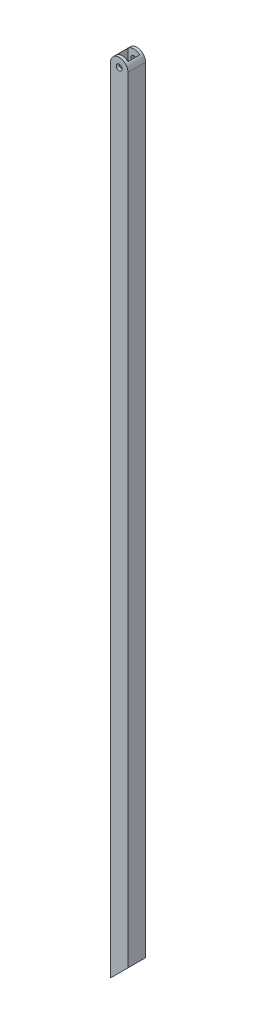
SolidWorks part; units mm, degrees
material "6061-T6 (SS)"
ref_plane "Plan de face" through (0, 0, 0) normal (0, 0, 1) x (1, 0, 0)
ref_plane "Plan de dessus" through (0, 0, 0) normal (0, 1, 0) x (1, 0, 0)
ref_plane "Plan de droite" through (0, 0, 0) normal (1, 0, 0) x (0, 0, -1)
sketch "Esquisse1" plane through (0, 0, 0) normal (0, 0, 1) x (1, 0, 0)
  line L0 (0, 0) -> (19.05, 19.05)
  line L2 (0, 0) -> (0, 860.475)
  line L4 (19.05, 19.05) -> (19.05, 860.475)
  line L5 (0, 0) -> (50000, 0) construction
  arc A0 (19.05, 860.475) -> (0, 860.475) centre (9.525, 860.475) ccw
  circle A1 centre (9.525, 860.475) radius 3.175
  dimension "D2" = 9.525
  dimension "D5" = 6.35
  dimension "D1" = 860.475
  dimension "D3" = 45
  dimension "D4" = 19.05
extrude "Boss.-Extru.1" add sketch "Esquisse1" along normal blind 19.05
sketch "Esquisse2" plane through (0, 0, 0) normal (0, 1, 0) x (1, 0, 0)
  line L0 (0, -19.05) -> (0, 0) construction
  line L1 (3.175, -3.175) -> (15.875, -3.175)
  line L2 (3.175, -3.175) -> (3.175, -15.875)
  line L3 (3.175, -15.875) -> (15.875, -15.875)
  line L4 (15.875, -3.175) -> (15.875, -15.875)
  line L5 (19.05, 0) -> (0, 0) construction
  dimension "D1" = 3.175
  dimension "D2" = 3.175
  dimension "D3" = 12.7
extrude "Enlèv. mat.-Extru.3" cut sketch "Esquisse2" along normal through all
